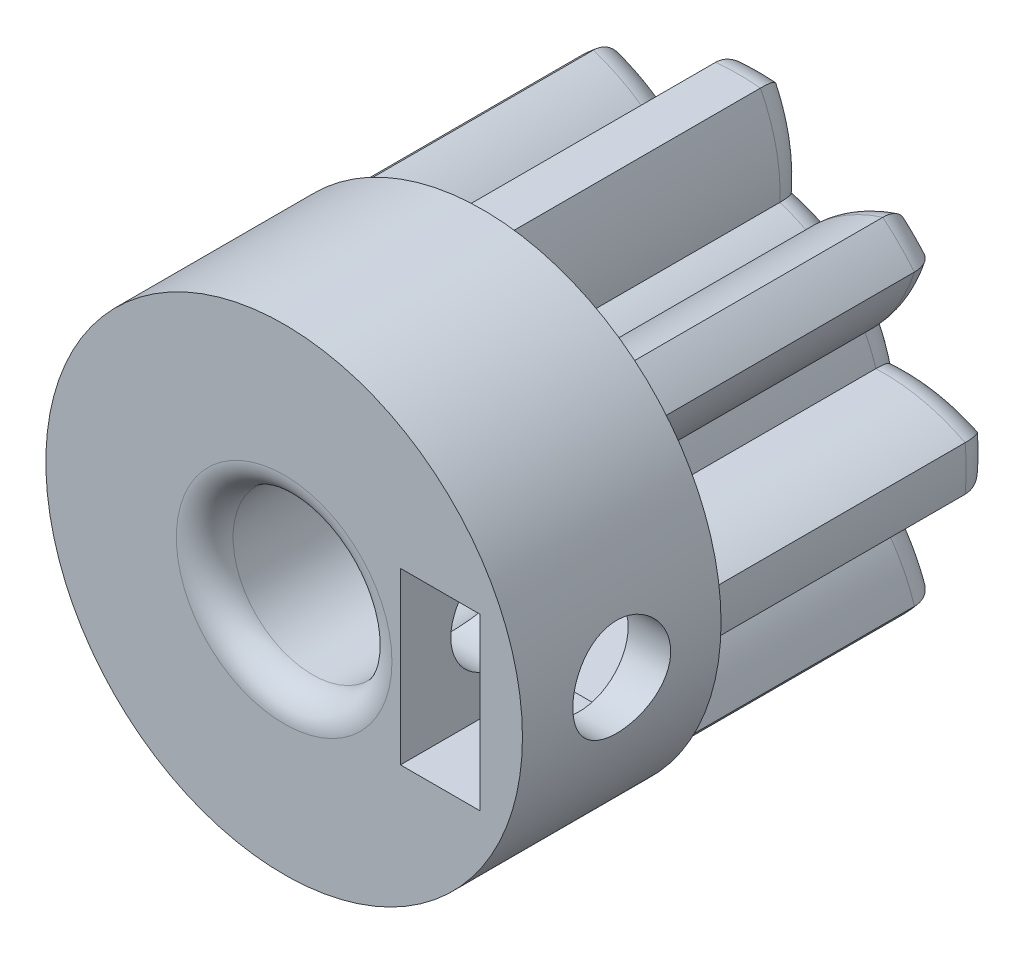
SolidWorks part; units mm, degrees
ref_plane "Alzado" through (0, 0, 0) normal (0, 0, 1) x (1, 0, 0)
ref_plane "Planta" through (0, 0, 0) normal (0, 1, 0) x (1, 0, 0)
ref_plane "Vista lateral" through (0, 0, 0) normal (1, 0, 0) x (0, 0, -1)
sketch "Croquis3" plane through (0, 0, 0) normal (0, 0, 1) x (1, 0, 0)
  circle A0 centre (0, 0) radius 8.4
  dimension "D1" = 16.8
extrude "Saliente-Extruir2" add sketch "Croquis3" against normal blind 7 separate body
sketch "Croquis4" plane through (0, 0, -7) normal (0, 0, -1) x (-1, 0, 0)
  line L0 (-0.7884, 8.0045) -> (1.4732, 4.8565) construction
  line L1 (-1.4732, 4.8565) -> (0.7884, 8.0045) construction
  line L2 (0.7884, 8.0045) -> (-0.7884, 8.0045) construction
  line L3 (0.7884, 8.0045) -> (1.4732, 4.8565) construction
  line L4 (-0.7884, 8.0045) -> (-1.4732, 4.8565) construction
  arc A0 (0.7884, 8.0045) -> (1.4732, 4.8565) centre (-4.7483, 5.1516) cw
  arc A1 (-1.4732, 4.8565) -> (-0.7884, 8.0045) centre (4.7352, 5.1544) cw
  arc A2 (-4.4757, 2.3923) -> (-4.8565, 1.4732) centre (0, 0) ccw
  arc A3 (-0.7884, 8.0045) -> (0.7884, 8.0045) centre (0, -0.0059) cw
  arc A4 (2.3923, 4.4757) -> (5.1025, 6.2175) centre (6.993, 0.2965) cw
  arc A5 (6.2175, 5.1025) -> (4.4757, 2.3923) centre (0.2851, 7.0003) cw
  arc A6 (5.1025, 6.2175) -> (6.2175, 5.1025) centre (-0.0042, -0.0042) cw
  arc A7 (4.8565, 1.4732) -> (8.0045, 0.7884) centre (5.1544, -4.7352) cw
  arc A8 (8.0045, -0.7884) -> (4.8565, -1.4732) centre (5.1516, 4.7483) cw
  arc A9 (8.0045, 0.7884) -> (8.0045, -0.7884) centre (-0.0059, 0) cw
  arc A10 (4.4757, -2.3923) -> (6.2175, -5.1025) centre (0.2965, -6.993) cw
  arc A11 (5.1025, -6.2175) -> (2.3923, -4.4757) centre (7.0003, -0.2851) cw
  arc A12 (6.2175, -5.1025) -> (5.1025, -6.2175) centre (-0.0042, 0.0042) cw
  arc A13 (1.4732, -4.8565) -> (0.7884, -8.0045) centre (-4.7352, -5.1544) cw
  arc A14 (-0.7884, -8.0045) -> (-1.4732, -4.8565) centre (4.7483, -5.1516) cw
  arc A15 (0.7884, -8.0045) -> (-0.7884, -8.0045) centre (0, 0.0059) cw
  arc A16 (-2.3923, -4.4757) -> (-5.1025, -6.2175) centre (-6.993, -0.2965) cw
  arc A17 (-6.2175, -5.1025) -> (-4.4757, -2.3923) centre (-0.2851, -7.0003) cw
  arc A18 (-5.1025, -6.2175) -> (-6.2175, -5.1025) centre (0.0042, 0.0042) cw
  arc A19 (-4.8565, -1.4732) -> (-8.0045, -0.7884) centre (-5.1544, 4.7352) cw
  arc A20 (-8.0045, 0.7884) -> (-4.8565, 1.4732) centre (-5.1516, -4.7483) cw
  arc A21 (-8.0045, -0.7884) -> (-8.0045, 0.7884) centre (0.0059, 0) cw
  arc A22 (-4.4757, 2.3923) -> (-6.2175, 5.1025) centre (-0.2965, 6.993) cw
  arc A23 (-5.1025, 6.2175) -> (-2.3923, 4.4757) centre (-7.0003, 0.2851) cw
  arc A24 (-6.2175, 5.1025) -> (-5.1025, 6.2175) centre (0.0042, -0.0042) cw
  arc A25 (-1.4732, 4.8565) -> (-2.3923, 4.4757) centre (0, 0) ccw
  arc A26 (2.3923, 4.4757) -> (1.4732, 4.8565) centre (0, 0) ccw
  arc A27 (4.8565, 1.4732) -> (4.4757, 2.3923) centre (0, 0) ccw
  arc A28 (4.4757, -2.3923) -> (4.8565, -1.4732) centre (0, 0) ccw
  arc A29 (1.4732, -4.8565) -> (2.3923, -4.4757) centre (0, 0) ccw
  arc A30 (-2.3923, -4.4757) -> (-1.4732, -4.8565) centre (0, 0) ccw
  arc A31 (-4.8565, -1.4732) -> (-4.4757, -2.3923) centre (0, 0) ccw
  point P71 (0, 0)
  dimension "D2" = 5.075
  dimension "D3" = 6.2285
  dimension "D4" = 6.2155
  dimension "D5" = 8.0491
  dimension "D8" = 1.5768
  dimension "D6" = 3.8762
  dimension "D7" = 3.8762
  dimension "D9" = 3.2216
  dimension "D10" = 3.148
  dimension "D1" = 8
extrude "Saliente-Extruir3" add sketch "Croquis4" along normal blind 10
fillet "Redondeo1" radius 1 32 edges at (3.6329, 5.5249, -17) (1.9421, 4.6887, -17) (1.3383, 6.4756, -17) (0, 8.0432, -17) (-1.3378, 6.4755, -17) (-1.9421, 4.6887, -17) (-3.6326, 5.5253, -17) (-5.6874, 5.6874, -17) (-5.5249, 3.6329, -17) (-4.6887, 1.9421, -17) (-6.4756, 1.3383, -17) (-8.0432, 0, -17) (-6.4755, -1.3378, -17) (-4.6887, -1.9421, -17) (-5.5253, -3.6326, -17) (-5.6874, -5.6874, -17) (-3.6329, -5.5249, -17) (-1.9421, -4.6887, -17) (-1.3383, -6.4756, -17) (0, -8.0432, -17) (1.3378, -6.4755, -17) (1.9421, -4.6887, -17) (3.6326, -5.5253, -17) (5.6874, -5.6874, -17) (5.5249, -3.6329, -17) (4.6887, -1.9421, -17) (6.4756, -1.3383, -17) (8.0432, 0, -17) (6.4755, 1.3378, -17) (4.6887, 1.9421, -17) (5.5253, 3.6326, -17) (5.6874, 5.6874, -17)
sketch "Croquis5" plane through (0, 0, 0) normal (0, 0, 1) x (1, 0, 0)
  circle A0 centre (0, 0) radius 2.8
  dimension "D1" = 5.6
extrude "Cortar-Extruir1" cut sketch "Croquis5" against normal through all
fillet "Redondeo2" radius 1 1 edges at (2.8, 0, 0)
sketch "Croquis6" plane through (0, 0, 0) normal (0, 0, 1) x (1, 0, 0)
  line L0 (4.1, 3) -> (6.9, 3)
  line L1 (6.9, -3) -> (6.9, 3)
  line L2 (4, -3.1) -> (7, -3.1) construction
  line L3 (4, -3.1) -> (4, 3.1) construction
  line L4 (4, 3.1) -> (7, 3.1) construction
  line L5 (7, -3.1) -> (7, 3.1) construction
  line L6 (4.1, -3) -> (6.9, -3)
  line L7 (4.1, -3) -> (4.1, 3)
  circle A0 centre (0, 0) radius 2.8 construction
  point P2 (0, 0)
  point P4 (4.9, 0)
  point P12 (0, 0)
  dimension "D2" = 4
  dimension "D3" = 3
  dimension "D4" = 6.2
  dimension "D5" = 3.1
  dimension "D1" = 0.1
extrude "Cortar-Extruir2" cut sketch "Croquis6" against normal blind 5.2898
sketch "Croquis7" plane through (4.1, 0, 0) normal (1, 0, 0) x (0, 0, -1)
  line L0 (5.2898, 3) -> (7.0796, 0)
  line L1 (7.0796, 0) -> (5.2898, -3)
  line L2 (5.2898, -3) -> (5.2898, 3)
  dimension "D1" = 1.7898
extrude "Cortar-Extruir3" cut sketch "Croquis7" along normal up to surface (2.8 mm away) up to face at (6.9, 0, -2.6449)
ref_plane "Plano2" through (8.4, 0, 0) normal (1, 0, 0) x (0, 0, -1)
sketch "Croquis8" plane through (8.4, 0, 0) normal (1, 0, 0) x (0, 0, -1)
  line L0 (0, 8.4) -> (0, -8.4) construction
  circle A0 centre (3.5, 0) radius 1.725
  dimension "D1" = 3.45
  dimension "D2" = 3.5
  dimension "D3" = 3
extrude "Cortar-Extruir4" cut sketch "Croquis8" against normal blind 7.2898
